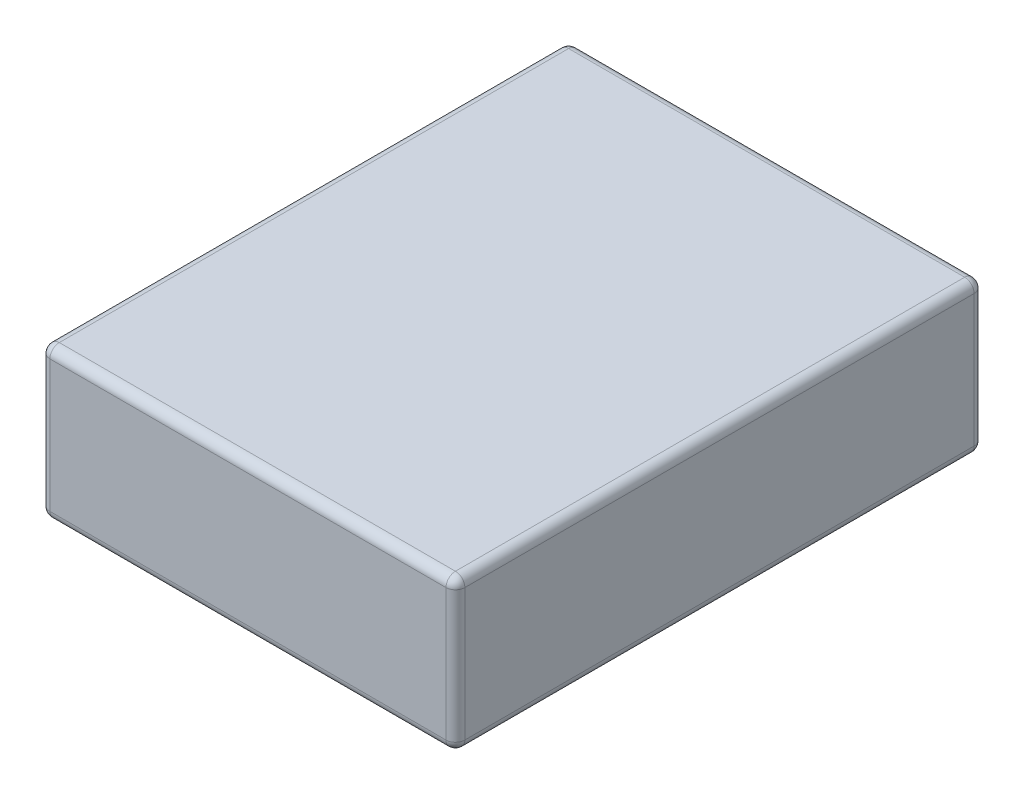
SolidWorks part; units mm, degrees
ref_plane "前视基准面" through (0, 0, 0) normal (0, 0, 1) x (1, 0, 0)
ref_plane "上视基准面" through (0, 0, 0) normal (0, 1, 0) x (1, 0, 0)
ref_plane "右视基准面" through (0, 0, 0) normal (1, 0, 0) x (0, 0, -1)
sketch "草图1" plane through (0, 0, 0) normal (0, 1, 0) x (1, 0, 0)
  line L1 (11, 14) -> (-11, 14)
  line L2 (11, 14) -> (11, -14)
  line L3 (11, -14) -> (-11, -14)
  line L4 (-11, 14) -> (-11, -14)
  line L5 (0, -14) -> (0, 14) construction
  line L6 (11, 0) -> (-11, 0) construction
  point P0 (0, 0)
  dimension "D1" = 22
  dimension "D2" = 28
extrude "凸台-拉伸1" add sketch "草图1" along normal blind 8
fillet "圆角1" radius 0.5 12 edges at (-11, 0, 0) (-11, 4, -14) (0, 0, -14) (11, 4, -14) (11, 0, 0) (-11, 4, 14) (11, 4, 14) (0, 0, 14) (0, 8, -14) (11, 8, 0) (0, 8, 14) (-11, 8, 0)
